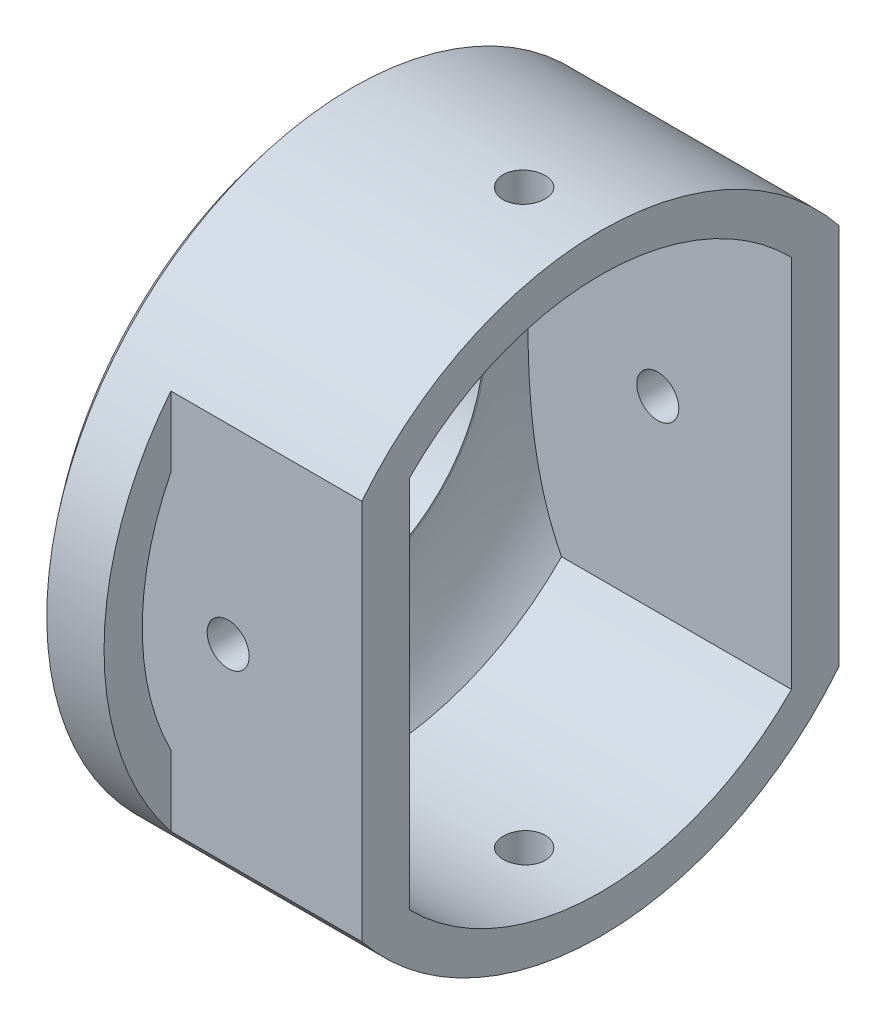
SolidWorks part; units mm, degrees
ref_plane "Front" through (0, 0, 0) normal (0, 0, 1) x (1, 0, 0)
ref_plane "Top" through (0, 0, 0) normal (0, 1, 0) x (1, 0, 0)
ref_plane "Right" through (0, 0, 0) normal (1, 0, 0) x (0, 0, -1)
sketch "Sketch1" plane through (0, 0, 0) normal (0, 0, 1) x (1, 0, 0)
  line L0 (0, 0) -> (0, 16)
  line L1 (0, 0) -> (-6, 0)
  line L2 (-6, 0) -> (-6, 8)
  line L3 (0, 16) -> (-3, 16)
  arc A1 (-3, 16) -> (-6, 8) centre (6.1667, 8) ccw
  dimension "D2" = 8
  dimension "D3" = 6
  dimension "D1" = 16
  dimension "D4" = 3
revolve "Revolve1" add sketch "Sketch1" angle 360 about L1
shell "Shell1" thickness 2
sketch "Sketch2" plane through (-4, 0, 0) normal (1, 0, 0) x (0, 0, -1)
  circle A0 centre (0, 0) radius 7.9
  dimension "D1" = 15.8
extrude "Cut-Extrude1" cut sketch "Sketch2" against normal up to next
sketch "Sketch3" plane through (0, 0, 0) normal (1, 0, 0) x (0, 0, -1)
  line L1 (-10, 9.9875) -> (-12.5, 9.9875)
  line L2 (-10, 9.9875) -> (-10, -9.9875)
  line L3 (-10, -9.9875) -> (-12.5, -9.9875)
  line L4 (-12.5, 9.9875) -> (-12.5, -9.9875)
  line L5 (-10, 9.9875) -> (-12.5, -9.9875) construction
  line L6 (-10, -9.9875) -> (-12.5, 9.9875) construction
  line L7 (10, 9.9875) -> (12.5, 9.9875)
  line L8 (10, 9.9875) -> (10, -9.9875)
  line L9 (10, -9.9875) -> (12.5, -9.9875)
  line L10 (12.5, 9.9875) -> (12.5, -9.9875)
  line L11 (10, 9.9875) -> (12.5, -9.9875) construction
  line L12 (10, -9.9875) -> (12.5, 9.9875) construction
  circle A1 centre (0, 0) radius 16 construction
  point P4 (-11.25, 0)
  point P14 (11.25, 0)
  circle M11 centre (0, 0) radius 14
  dimension "D1" = 10
  dimension "D2" = 2.5
  dimension "D3" = 10
  dimension "D4" = 2.5
extrude "Boss-Extrude1" add sketch "Sketch3" along normal blind 10 and the other way up to surface contours L4 L2 M11 | L10 L8 M11 | L1 L4 L2 M11 | L4 L3 L2 M11 | L10 L8 L9 M11 | L10 L7 L8 M11
sketch "Sketch4" plane through (0, 0, 12.5) normal (0, 0, 1) x (1, 0, 0)
  line L1 (-6, 8) -> (-6, -8) construction
  circle A0 centre (3, 0) radius 1.1
  dimension "D1" = 2.2
  dimension "D2" = 9
extrude "Cut-Extrude2" cut sketch "Sketch4" against normal through all
sketch "Sketch5" plane through (0, 0, 0) normal (1, 0, 0) x (0, 0, -1)
  line L20 (10, 9.798) -> (10, 9.9875)
  line L21 (10, 9.9875) -> (12.5, 9.9875)
  line L22 (-12.5, 9.9875) -> (-10, 9.9875)
  line L23 (-10, 9.9875) -> (-10, 9.798)
  line L24 (10, 9.798) -> (10, 9.9875)
  line L25 (10, 9.9875) -> (12.5, 9.9875)
  line L26 (-12.5, 9.9875) -> (-10, 9.9875)
  line L27 (-10, 9.9875) -> (-10, 9.798)
  line L28 (12.5, -9.9875) -> (10, -9.9875)
  line L29 (10, -9.9875) -> (10, -9.798)
  line L30 (-10, -9.798) -> (-10, -9.9875)
  line L31 (-10, -9.9875) -> (-12.5, -9.9875)
  line L32 (12.5, -9.9875) -> (10, -9.9875)
  line L33 (10, -9.9875) -> (10, -9.798)
  line L34 (-10, -9.798) -> (-10, -9.9875)
  line L35 (-10, -9.9875) -> (-12.5, -9.9875)
  arc A26 (12.5, 9.9875) -> (-12.5, 9.9875) centre (0, 0) ccw
  arc A27 (10, 9.798) -> (-10, 9.798) centre (0, 0) ccw
  arc A28 (12.5, 9.9875) -> (-12.5, 9.9875) centre (0, 0) ccw
  arc A29 (10, 9.798) -> (-10, 9.798) centre (0, 0) ccw
  arc A30 (-10, -9.798) -> (10, -9.798) centre (0, 0) ccw
  arc A31 (-12.5, -9.9875) -> (12.5, -9.9875) centre (0, 0) ccw
  arc A32 (-10, -9.798) -> (10, -9.798) centre (0, 0) ccw
  arc A33 (-12.5, -9.9875) -> (12.5, -9.9875) centre (0, 0) ccw
  dimension "D1" = 0
  dimension "D2" = 0
extrude "Boss-Extrude3" add sketch "Sketch5" along normal blind 10
sketch "Sketch6" plane through (0, 0, 0) normal (0, 1, 0) x (1, 0, 0)
  line L1 (-6, 8) -> (-6, -8) construction
  circle A0 centre (6, 0) radius 1.1
  dimension "D1" = 2.2
  dimension "D2" = 12
extrude "Cut-Extrude3" cut sketch "Sketch6" against normal mid plane 45 contours A0
